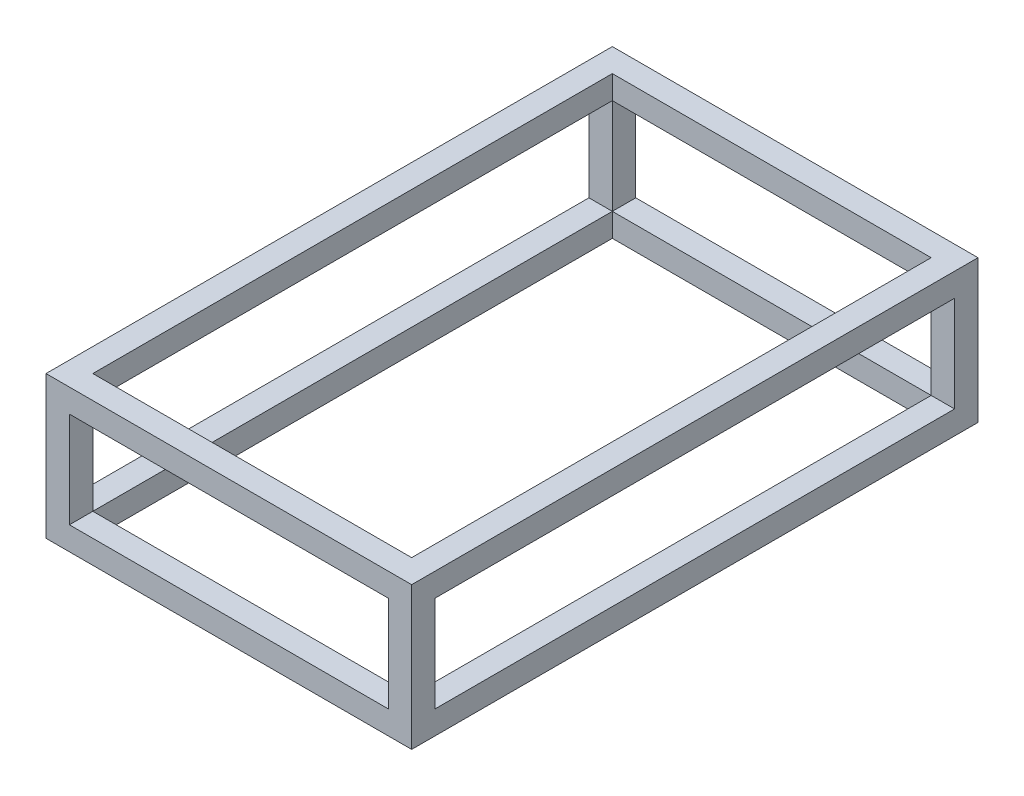
SolidWorks part; units mm, degrees
ref_plane "Front Plane" through (0, 0, 0) normal (0, 0, 1) x (1, 0, 0)
ref_plane "Top Plane" through (0, 0, 0) normal (0, 1, 0) x (1, 0, 0)
ref_plane "Right Plane" through (0, 0, 0) normal (1, 0, 0) x (0, 0, -1)
sketch "Sketch2" plane through (0, 0, 0) normal (0, 0, 1) x (1, 0, 0)
  line L1 (-25, -25) -> (25, -25)
  line L2 (-25, -25) -> (-25, 25)
  line L3 (-25, 25) -> (25, 25)
  line L4 (25, -25) -> (25, 25)
  line L5 (-25, -25) -> (25, 25) construction
  line L6 (-25, 25) -> (25, -25) construction
  point P0 (0, 0)
  dimension "D1" = 50
  dimension "D2" = 50
extrude "Boss-Extrude1" add sketch "Sketch2" along normal blind 1209.675
sketch "Sketch3" plane through (25, 0, 0) normal (1, 0, 0) x (0, 0, -1)
  line L0 (-1209.675, -25) -> (0, -25) construction
  line L1 (-1209.675, 25) -> (-1159.675, 25)
  line L2 (-1209.675, 25) -> (-1209.675, -25)
  line L3 (-1209.675, -25) -> (-1159.675, -25)
  line L4 (-1159.675, 25) -> (-1159.675, -25)
  dimension "D1" = 50
extrude "Boss-Extrude2" add sketch "Sketch3" along normal blind 731.05
sketch "Sketch4" plane through (0, 0, 1159.675) normal (0, 0, -1) x (-1, 0, 0)
  line L0 (-756.05, -25) -> (-25, -25) construction
  line L1 (-756.05, 25) -> (-706.05, 25)
  line L2 (-756.05, 25) -> (-756.05, -25)
  line L3 (-756.05, -25) -> (-706.05, -25)
  line L4 (-706.05, 25) -> (-706.05, -25)
  dimension "D1" = 50
extrude "Boss-Extrude3" add sketch "Sketch4" along normal blind 1159.68
sketch "Sketch6" plane through (706.05, 0, 0) normal (-1, 0, 0) x (0, 0, 1)
  line L0 (-0.005, -25) -> (1159.675, -25) construction
  line L1 (-0.005, 25) -> (49.995, 25)
  line L2 (-0.005, 25) -> (-0.005, -25)
  line L3 (-0.005, -25) -> (49.995, -25)
  line L4 (49.995, 25) -> (49.995, -25)
  dimension "D1" = 50
extrude "Boss-Extrude4" add sketch "Sketch6" along normal blind 681.05
sketch "Sketch8" plane through (0, 25, 0) normal (0, 1, 0) x (1, 0, 0)
  line L1 (25, -1159.675) -> (-25, -1159.675)
  line L2 (25, -1159.675) -> (25, -1209.675)
  line L3 (25, -1209.675) -> (-25, -1209.675)
  line L4 (-25, -1159.675) -> (-25, -1209.675)
extrude "Boss-Extrude5" add sketch "Sketch8" along normal blind 254.8
sketch "Sketch9" plane through (25, 0, 0) normal (1, 0, 0) x (0, 0, -1)
  line L0 (-1159.675, 279.8) -> (-1159.675, 25) construction
  line L1 (-1209.675, 279.8) -> (-1159.675, 279.8)
  line L2 (-1209.675, 279.8) -> (-1209.675, 229.8)
  line L3 (-1209.675, 229.8) -> (-1159.675, 229.8)
  line L4 (-1159.675, 279.8) -> (-1159.675, 229.8)
  dimension "D1" = 50
extrude "Boss-Extrude6" add sketch "Sketch9" along normal blind 731.05
sketch "Sketch10" plane through (0, 229.8, 0) normal (0, -1, 0) x (1, 0, 0)
  line L0 (756.05, 1159.675) -> (25, 1159.675) construction
  line L1 (756.05, 1209.675) -> (706.05, 1209.675)
  line L2 (756.05, 1209.675) -> (756.05, 1159.675)
  line L3 (756.05, 1159.675) -> (706.05, 1159.675)
  line L4 (706.05, 1209.675) -> (706.05, 1159.675)
  dimension "D1" = 50
extrude "Boss-Extrude7" add sketch "Sketch10" along normal blind 204.8
sketch "Sketch11" plane through (0, 25, 0) normal (0, 1, 0) x (1, 0, 0)
  line L0 (-167.64, 0) -> (167.64, 0) construction
  line L1 (706.05, -49.995) -> (756.05, -49.995)
  line L2 (706.05, -49.995) -> (706.05, 0)
  line L3 (706.05, 0) -> (756.05, 0)
  line L4 (756.05, -49.995) -> (756.05, 0)
  line L5 (756.05, 0.005) -> (756.05, -1159.675) construction
extrude "Boss-Extrude8" add sketch "Sketch11" along normal blind 254.8
sketch "Sketch12" plane through (0, 0, 1159.675) normal (0, 0, -1) x (-1, 0, 0)
  line L1 (-706.05, 229.8) -> (-756.05, 229.8)
  line L2 (-706.05, 229.8) -> (-706.05, 279.8)
  line L3 (-706.05, 279.8) -> (-756.05, 279.8)
  line L4 (-756.05, 229.8) -> (-756.05, 279.8)
extrude "Boss-Extrude9" add sketch "Sketch12" along normal blind 1109.8
sketch "Sketch13" plane through (0, 0, 1159.675) normal (0, 0, -1) x (-1, 0, 0)
  line L1 (-25, 229.8) -> (25, 229.8)
  line L2 (-25, 229.8) -> (-25, 279.8)
  line L3 (-25, 279.8) -> (25, 279.8)
  line L4 (25, 229.8) -> (25, 279.8)
extrude "Boss-Extrude10" add sketch "Sketch13" along normal blind 1109.8
sketch "Sketch14" plane through (0, 25, 0) normal (0, 1, 0) x (1, 0, 0)
  line L0 (-167.64, 0) -> (167.64, 0) construction
  line L1 (-25, 0) -> (25, 0)
  line L2 (-25, 0) -> (-25, -49.995)
  line L3 (-25, -49.995) -> (25, -49.995)
  line L4 (25, 0) -> (25, -49.995)
  line L5 (-25, -1159.675) -> (-25, 0) construction
extrude "Boss-Extrude11" add sketch "Sketch14" along normal blind 254.8
sketch "Sketch15" plane through (25, 0, 0) normal (1, 0, 0) x (0, 0, -1)
  line L1 (-49.995, 229.8) -> (0, 229.8)
  line L2 (-49.995, 229.8) -> (-49.995, 279.8)
  line L3 (-49.995, 279.8) -> (0, 279.8)
  line L4 (0, 229.8) -> (0, 279.8)
extrude "Boss-Extrude12" add sketch "Sketch15" along normal blind 681.05
